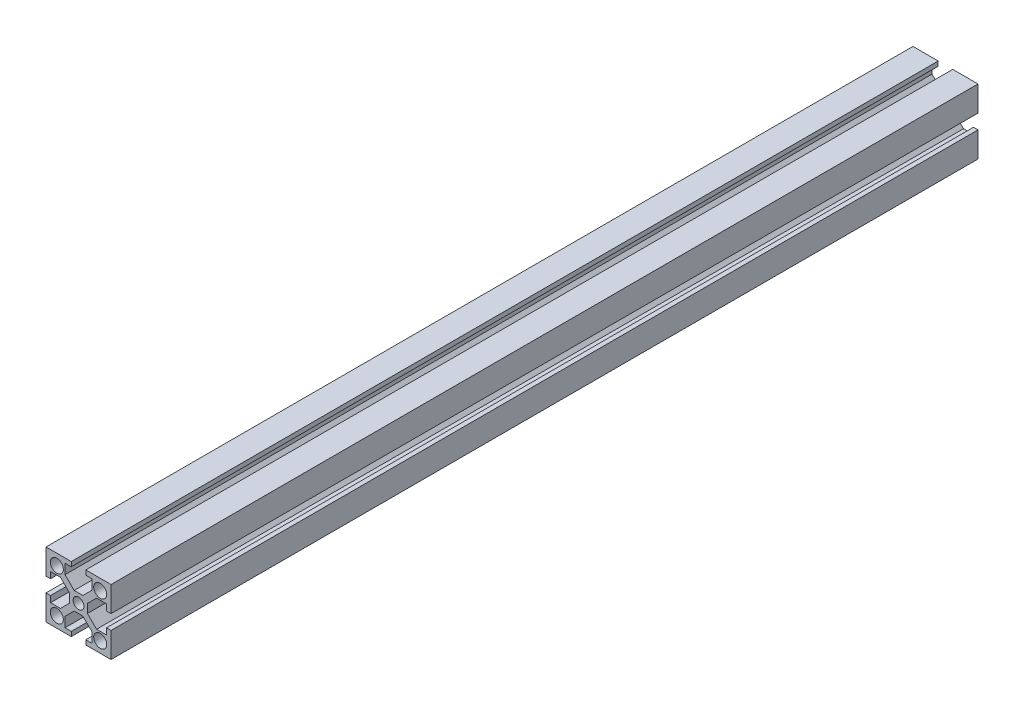
SolidWorks part; units mm, degrees
ref_plane "Front Plane" through (0, 0, 0) normal (0, 0, 1) x (1, 0, 0)
ref_plane "Top Plane" through (0, 0, 0) normal (0, 1, 0) x (1, 0, 0)
ref_plane "Right Plane" through (0, 0, 0) normal (1, 0, 0) x (0, 0, -1)
sketch "Sketch1" plane through (0, 0, 0) normal (0, 0, 1) x (1, 0, 0)
  line L0 (0, 10) -> (0, -10) construction
  line L1 (-15, -15) -> (15, -15) construction
  line L2 (-15, -15) -> (-15, 15) construction
  line L3 (-15, 15) -> (15, 15) construction
  line L4 (15, -15) -> (15, 15) construction
  line L5 (-10, -10) -> (10, -10) construction
  line L6 (-10, -10) -> (-10, 10) construction
  line L7 (-10, 10) -> (10, 10) construction
  line L8 (10, -10) -> (10, 10) construction
  line L9 (10, 0) -> (-10, 0) construction
  line L10 (-15, 15) -> (-3.35, 15)
  line L11 (-3.35, 15) -> (-3.35, 12.902)
  line L12 (-3.35, 12.902) -> (-6.2165, 12.902)
  line L13 (-6.2165, 12.902) -> (-6.2165, 8.3232)
  line L14 (-6.2165, 8.3232) -> (-2.0187, 4.1254)
  line L15 (-4.1254, -4.1254) -> (4.1254, -4.1254) construction
  line L16 (-4.1254, -4.1254) -> (-4.1254, 4.1254) construction
  line L17 (-4.1254, 4.1254) -> (4.1254, 4.1254) construction
  line L18 (4.1254, -4.1254) -> (4.1254, 4.1254) construction
  line L19 (0, 4.1254) -> (0, -4.1254) construction
  line L20 (-4.1254, 0) -> (4.1254, 0) construction
  line L21 (-15, 15) -> (0, 0) construction
  line L22 (-8.3232, 6.2165) -> (-4.1254, 2.0187)
  line L23 (-12.902, 6.2165) -> (-8.3232, 6.2165)
  line L24 (-12.902, 3.35) -> (-12.902, 6.2165)
  line L25 (-15, 3.35) -> (-12.902, 3.35)
  line L26 (-15, 15) -> (-15, 3.35)
  line L27 (6.2165, 8.3232) -> (2.0187, 4.1254)
  line L28 (6.2165, 12.902) -> (6.2165, 8.3232)
  line L29 (3.35, 12.902) -> (6.2165, 12.902)
  line L30 (3.35, 15) -> (3.35, 12.902)
  line L31 (15, 15) -> (15, 3.35)
  line L32 (15, 3.35) -> (12.902, 3.35)
  line L33 (12.902, 3.35) -> (12.902, 6.2165)
  line L34 (12.902, 6.2165) -> (8.3232, 6.2165)
  line L35 (8.3232, 6.2165) -> (4.1254, 2.0187)
  line L36 (15, 15) -> (3.35, 15)
  line L37 (8.3232, -6.2165) -> (4.1254, -2.0187)
  line L38 (12.902, -6.2165) -> (8.3232, -6.2165)
  line L39 (12.902, -3.35) -> (12.902, -6.2165)
  line L40 (15, -3.35) -> (12.902, -3.35)
  line L41 (15, -15) -> (3.35, -15)
  line L42 (3.35, -15) -> (3.35, -12.902)
  line L43 (3.35, -12.902) -> (6.2165, -12.902)
  line L44 (6.2165, -12.902) -> (6.2165, -8.3232)
  line L45 (6.2165, -8.3232) -> (2.0187, -4.1254)
  line L46 (15, -15) -> (15, -3.35)
  line L47 (-6.2165, -8.3232) -> (-2.0187, -4.1254)
  line L48 (-6.2165, -12.902) -> (-6.2165, -8.3232)
  line L49 (-3.35, -12.902) -> (-6.2165, -12.902)
  line L50 (-3.35, -15) -> (-3.35, -12.902)
  line L51 (-15, -15) -> (-15, -3.35)
  line L52 (-15, -3.35) -> (-12.902, -3.35)
  line L53 (-12.902, -3.35) -> (-12.902, -6.2165)
  line L54 (-12.902, -6.2165) -> (-8.3232, -6.2165)
  line L55 (-8.3232, -6.2165) -> (-4.1254, -2.0187)
  line L56 (-15, -15) -> (-3.35, -15)
  line L57 (-2.0187, 4.1254) -> (2.0187, 4.1254)
  line L58 (4.1254, 2.0187) -> (4.1254, -2.0187)
  line L59 (2.0187, -4.1254) -> (-2.0187, -4.1254)
  line L60 (-4.1254, -2.0187) -> (-4.1254, 2.0187)
  circle A0 centre (0, 0) radius 2.5
  circle A1 centre (10, 10) radius 3
  circle A3 centre (-10, 10) radius 3
  circle A4 centre (-10, -10) radius 3
  circle A5 centre (10, -10) radius 3
  point P0 (0, 0)
  point P17 (0, 0)
  point P67 (0, 0)
  dimension "D2" = 5
  dimension "D3" = 6
  dimension "D1" = 30
  dimension "D4" = 20
  dimension "D5" = 11.65
  dimension "D6" = 4
extrude "Boss-Extrude1" add sketch "Sketch1" along normal blind 400
